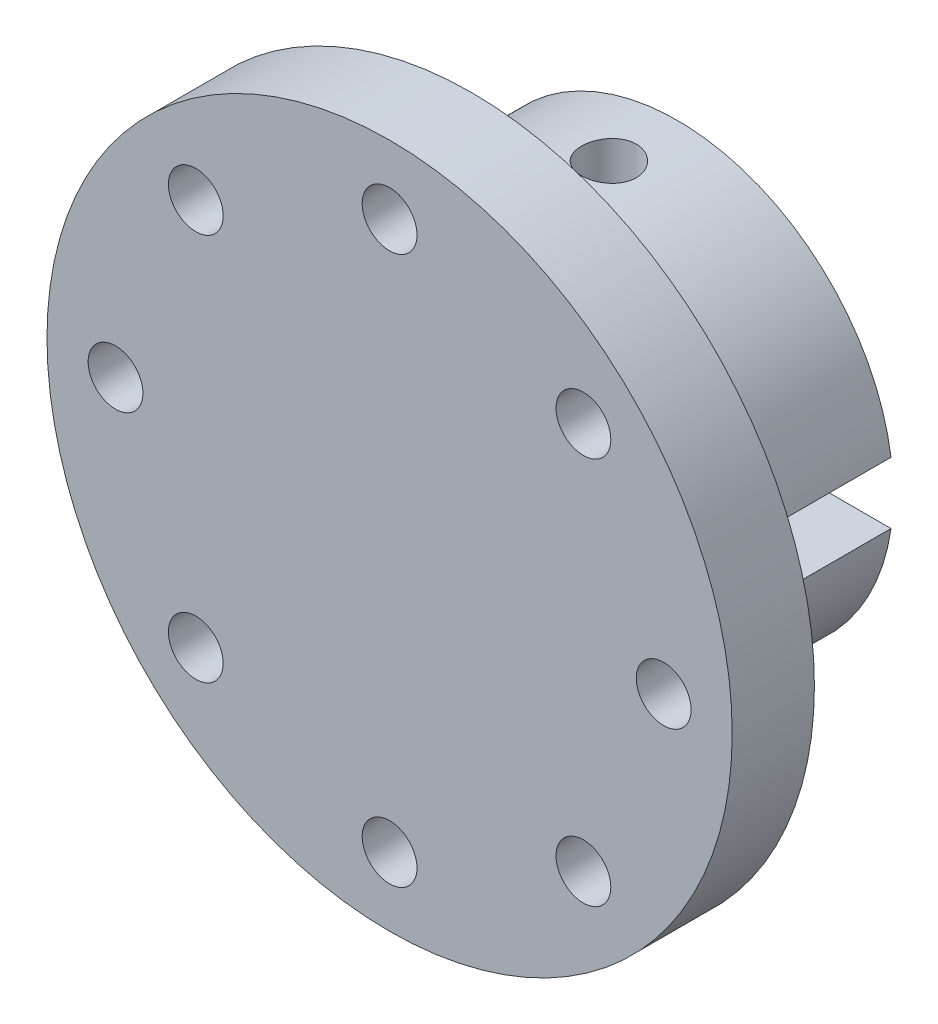
SolidWorks part; units mm, degrees
material "AISI 1020"
ref_plane "Plano frontal" through (0, 0, 0) normal (0, 0, 1) x (1, 0, 0)
ref_plane "Plano superior" through (0, 0, 0) normal (0, 1, 0) x (1, 0, 0)
ref_plane "Plano direito" through (0, 0, 0) normal (1, 0, 0) x (0, 0, -1)
sketch "Esboço1" plane through (0, 0, 0) normal (0, 0, 1) x (1, 0, 0)
  line L0 (-14.5, 4.5) -> (-31.1769, 4.5)
  line L5 (-28.1587, -28.4093) -> (28.1587, 28.4093) construction
  line L6 (-28.1587, 28.4093) -> (28.1587, -28.4093) construction
  line L7 (-14.5, -4.5) -> (14.5, -4.5)
  line L9 (-14.5, 4.5) -> (14.5, 4.5)
  line L11 (-14.5, -4.5) -> (14.5, 4.5) construction
  line L12 (-14.5, 4.5) -> (14.5, -4.5) construction
  line L13 (14.5, 4.5) -> (31.1769, 4.5)
  line L14 (14.5, -4.5) -> (31.1769, -4.5)
  line L15 (-14.5, -4.5) -> (-31.1769, -4.5)
  arc A1 (-31.1769, -4.5) -> (31.1769, -4.5) centre (0, 0) ccw
  arc A13 (31.1769, 4.5) -> (-31.1769, 4.5) centre (0, 0) ccw
  dimension "D1" = 63
  dimension "D3" = 9
extrude "Ressalto-extrusão1" add sketch "Esboço1" along normal blind 30
sketch "Esboço2" plane through (0, 0, 0) normal (0, 1, 0) x (1, 0, 0)
  line L0 (31.1769, 0) -> (-31.1769, 0) construction
  circle A0 centre (0, -10) radius 4
  dimension "D1" = 10
  dimension "D2" = 8
extrude "Corte-extrusão1" cut sketch "Esboço2" against normal mid plane 100
sketch "Esboço6" plane through (0, 0, 30) normal (0, 0, 1) x (1, 0, 0)
  line L5 (-28.2843, 28.2843) -> (28.2843, -28.2843) construction
  line L6 (-28.2843, -28.2843) -> (28.2843, 28.2843) construction
  circle A0 centre (0, 0) radius 50
  circle A2 centre (40, 0) radius 4
  circle A3 centre (-40, 0) radius 4
  circle A4 centre (-28.2843, 28.2843) radius 4
  circle A5 centre (-28.2843, -28.2843) radius 4
  circle A6 centre (28.2843, -28.2843) radius 4
  circle A7 centre (28.2843, 28.2843) radius 4
  circle A9 centre (0, 40) radius 4
  circle A10 centre (0, -40) radius 4
  dimension "D1" = 90
extrude "Ressalto-extrusão2" add sketch "Esboço6" along normal blind 12
